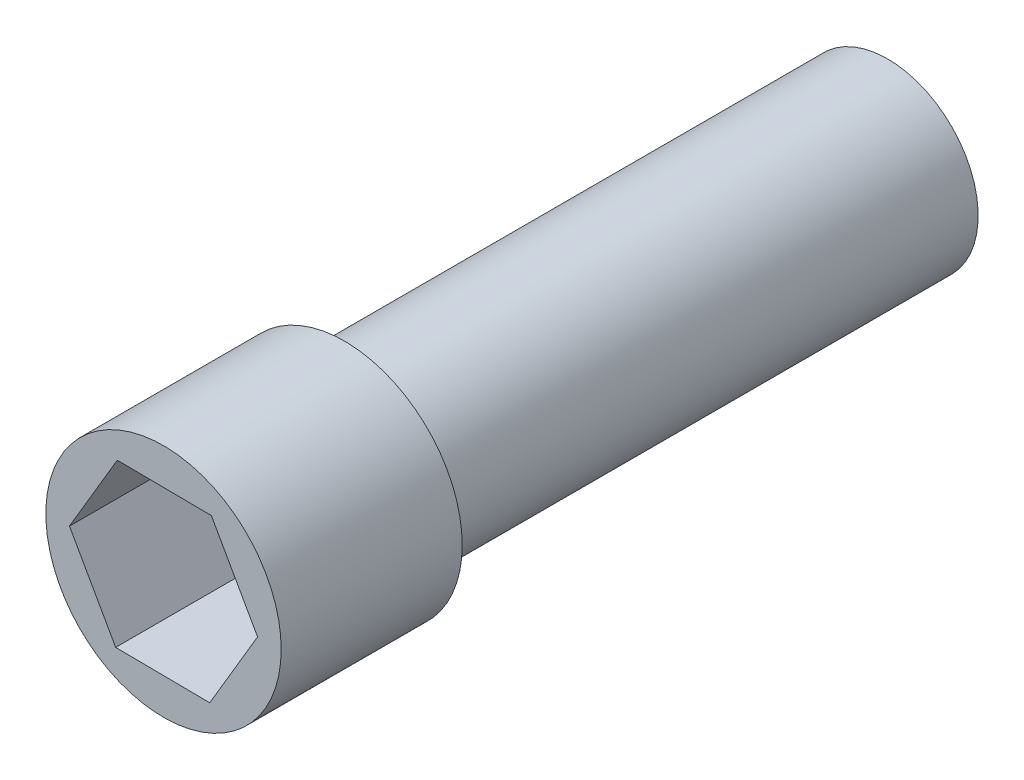
SolidWorks part; units mm, degrees
material "AISI 321 Annealed Stainless Steel (SS)"
ref_plane "Front Plane" through (0, 0, 0) normal (0, 0, 1) x (1, 0, 0)
ref_plane "Top Plane" through (0, 0, 0) normal (0, 1, 0) x (1, 0, 0)
ref_plane "Right Plane" through (0, 0, 0) normal (1, 0, 0) x (0, 0, -1)
sketch "Sketch1" plane through (0, 0, 0) normal (0, 0, 1) x (1, 0, 0)
  circle A0 centre (0, 0) radius 6.5
  dimension "D1" = 13
extrude "Boss-Extrude1" add sketch "Sketch1" against normal blind 10
sketch "Sketch2" plane through (0, 0, -10) normal (0, 0, -1) x (-1, 0, 0)
  circle A0 centre (0, 0) radius 5
  dimension "D1" = 10
extrude "Boss-Extrude2" add sketch "Sketch2" along normal blind 30
sketch "Sketch3" plane through (0, 0, 0) normal (0, 0, 1) x (1, 0, 0)
  line L1 (-2.5528, 4.5258) -> (-5.1959, 0.0522)
  line L2 (-5.1959, 0.0522) -> (-2.6431, -4.4737)
  line L3 (-2.6431, -4.4737) -> (2.5528, -4.5258)
  line L4 (2.5528, -4.5258) -> (5.1959, -0.0522)
  line L5 (5.1959, -0.0522) -> (2.6431, 4.4737)
  line L6 (2.6431, 4.4737) -> (-2.5528, 4.5258)
  circle A0 centre (0, 0) radius 4.5 construction
  dimension "D1" = 9
extrude "Cut-Extrude1" cut sketch "Sketch3" against normal blind 9
